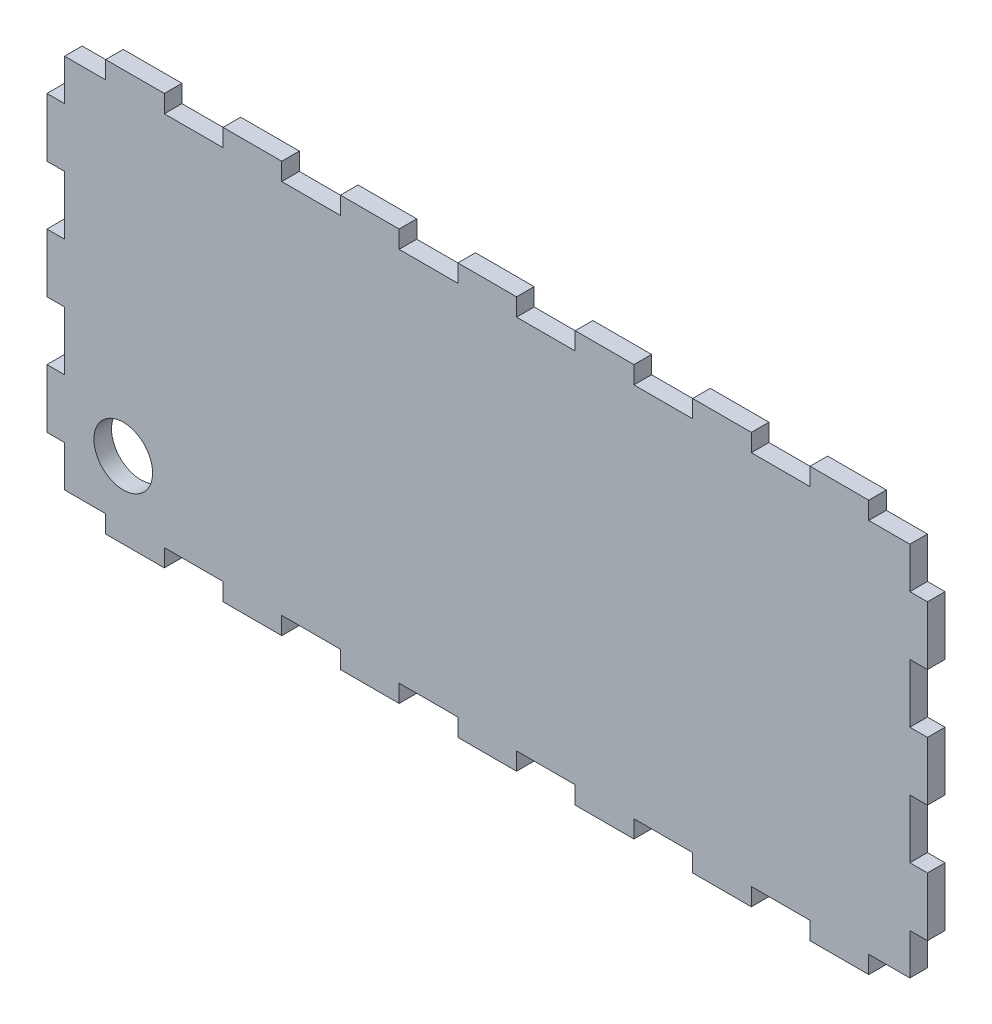
SolidWorks part; units mm, degrees
ref_plane "Front Plane" through (0, 0, 0) normal (0, 0, 1) x (1, 0, 0)
ref_plane "Top Plane" through (0, 0, 0) normal (0, 1, 0) x (1, 0, 0)
ref_plane "Right Plane" through (0, 0, 0) normal (1, 0, 0) x (0, 0, -1)
sketch "Sketch1" plane through (0, 0, 0) normal (0, 0, 1) x (1, 0, 0)
  line L1 (-75, 35) -> (75, 35)
  line L2 (-75, 35) -> (-75, -35)
  line L3 (-75, -35) -> (75, -35)
  line L4 (75, 35) -> (75, -35)
  line L5 (-75, 35) -> (75, -35) construction
  line L6 (-75, -35) -> (75, 35) construction
  point P0 (0, 0)
  dimension "D1" = 150
  dimension "D2" = 70
extrude "Boss-Extrude1" add sketch "Sketch1" along normal blind 3
sketch "Sketch2" plane through (0, 0, 3) normal (0, 0, 1) x (1, 0, 0)
  line L1 (-75, 35) -> (-65, 35)
  line L2 (-75, 35) -> (-75, 32)
  line L3 (-75, 32) -> (-65, 32)
  line L4 (-65, 35) -> (-65, 32)
  dimension "D1" = 3
  dimension "D2" = 10
extrude "Cut-Extrude1" cut sketch "Sketch2" against normal blind 3
pattern_linear "LPattern3" count 8 spacing 20 along (1, 0, 0) of "Cut-Extrude1"
mirror "Mirror1" about plane through (0, 0, 0) normal (0, 1, 0) of "LPattern3", "Cut-Extrude1"
sketch "Sketch3" plane through (0, 0, 3) normal (0, 0, 1) x (1, 0, 0)
  line L0 (-75, 32) -> (-75, -32) construction
  line L1 (-75, 25) -> (-72, 25)
  line L2 (-75, 25) -> (-75, 35)
  line L3 (-75, 35) -> (-72, 35)
  line L4 (-72, 25) -> (-72, 35)
  line L5 (-55, 35) -> (-65, 35) construction
  dimension "D1" = 10
  dimension "D2" = 3
extrude "Cut-Extrude2" cut sketch "Sketch3" against normal blind 3
pattern_linear "LPattern4" count 4 spacing 20 along (0, -1, 0) of "Cut-Extrude2"
mirror "Mirror2" about plane through (0, 0, 0) normal (1, 0, 0) of "LPattern4", "Cut-Extrude2"
sketch "Sketch6" plane through (0, 0, 0) normal (0, 0, -1) x (-1, 0, 0)
  line L0 (45, -35) -> (55, -35) construction
  line L2 (75, -15) -> (75, -25) construction
  circle A0 centre (62, -22) radius 5
  point P6 (75, -20.1272)
  dimension "D1" = 10
  dimension "D2" = 13
  dimension "D3" = 13
extrude "Cut-Extrude3" cut sketch "Sketch6" against normal blind 3
